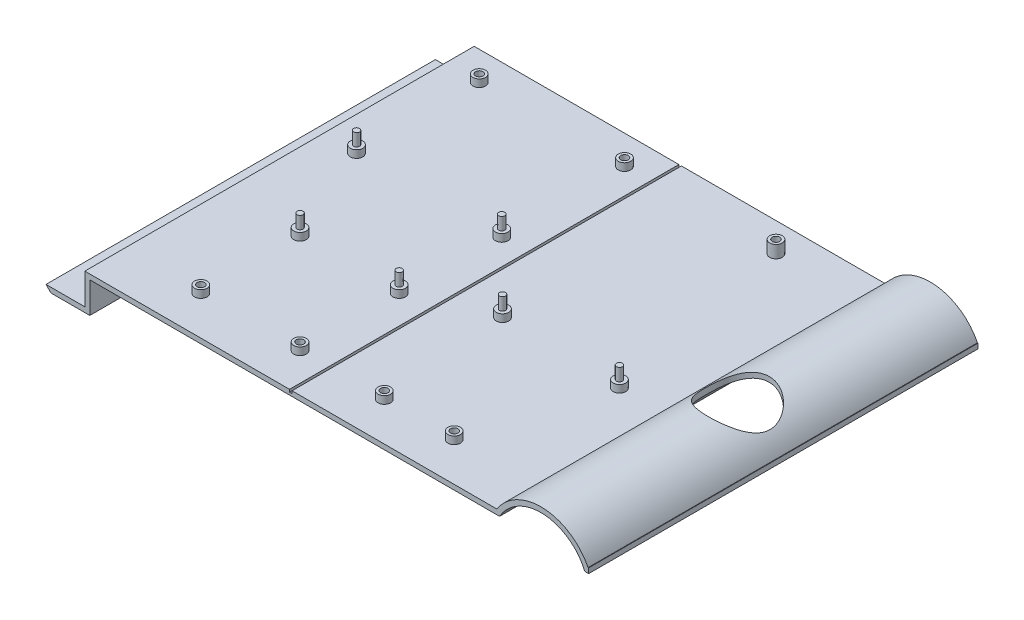
SolidWorks part; units mm, degrees
ref_plane "Ebene vorne" through (0, 0, 0) normal (0, 0, 1) x (1, 0, 0)
ref_plane "Ebene oben" through (0, 0, 0) normal (0, 1, 0) x (1, 0, 0)
ref_plane "Ebene rechts" through (0, 0, 0) normal (1, 0, 0) x (0, 0, -1)
sketch "Skizze5" plane through (0, 0, 0) normal (0, 0, 1) x (1, 0, 0)
  line L0 (0, 0) -> (158.2131, 0)
  line L2 (158.2131, 0) -> (163.627, 0)
  line L3 (0, 0) -> (0, -12.3404)
  line L4 (0, -12.3404) -> (-17.5, -12.3404)
  line L5 (197.6943, -2.0448) -> (199.1943, -2.0448)
  arc A5 (197.6943, -2.0448) -> (181.1299, 9.5495) centre (180.1533, -9.4754) ccw
  arc A6 (181.1299, 9.5495) -> (163.627, 0) centre (180.1533, -9.4754) ccw
  dimension "D1" = 1.5
  dimension "D2" = 17.5
extrude "Linear-Austragen-Dünn1" add sketch "Skizze5" along normal blind 155.5 thin contours L4 L3 L0 thin type one direction reverse wall 2
sketch "Skizze7" plane through (0.013, 0, 0) normal (0, 1, 0) x (1, 0, 0)
  circle A0 centre (11.5, -11.5) radius 2.5
  circle A1 centre (69.5, -11.5) radius 2.5
  circle A2 centre (11.5, -60.5) radius 2.5
  circle A3 centre (69.5, -60.5) radius 2.5
extrude "Aufsatz-Linear austragen3" add sketch "Skizze7" along normal blind 5
sketch "Skizze8" plane through (0, 5, 0) normal (0, 1, 0) x (1, 0, 0)
  circle A0 centre (11.513, -11.5) radius 1.5
extrude "Schnitt-Linear austragen1" cut sketch "Skizze8" against normal blind 8
sketch "Skizze10" plane through (0, 5, 0) normal (0, 1, 0) x (1, 0, 0)
  circle A0 centre (11.513, -60.5) radius 1.2
sketch "Skizze11" plane through (0, 5, 0) normal (0, 1, 0) x (1, 0, 0)
  circle A0 centre (69.513, -60.5) radius 1.2
sketch "Skizze12" plane through (0, 5, 0) normal (0, 1, 0) x (1, 0, 0)
  circle A0 centre (69.513, -11.5) radius 1.5
extrude "Schnitt-Linear austragen4" cut sketch "Skizze12" against normal blind 8
sketch "Skizze13" plane through (0.013, 0, 0) normal (0, 1, 0) x (1, 0, 0)
  line L0 (97.4, -88.1) -> (97.4, -87.1) construction
  line L1 (145.2, -89.2) -> (145.2, -88.2) construction
  line L2 (102.1, -140) -> (102.1, -139) construction
  line L3 (130, -140) -> (130, -139) construction
  circle A0 centre (130, -140) radius 2.5
  circle A1 centre (102.1, -140) radius 2.5
  circle A2 centre (145.2, -89.2) radius 2.5
  circle A3 centre (97.4, -88.1) radius 2.5
  dimension "D1" = 1
  dimension "D2" = 1
  dimension "D3" = 1
  dimension "D4" = 1
extrude "Aufsatz-Linear austragen5" add sketch "Skizze13" along normal blind 5
sketch "Skizze14" plane through (0, 5, 0) normal (0, 1, 0) x (1, 0, 0)
  circle A1 centre (145.213, -89.2) radius 1.2
sketch "Skizze15" plane through (0, 5, 0) normal (0, 1, 0) x (1, 0, 0)
  circle A0 centre (97.413, -88.1) radius 1.2
sketch "Skizze16" plane through (0, 5, 0) normal (0, 1, 0) x (1, 0, 0)
  circle A0 centre (102.113, -140) radius 1.5
extrude "Schnitt-Linear austragen9" cut sketch "Skizze16" against normal blind 8
sketch "Skizze17" plane through (0, 5, 0) normal (0, 1, 0) x (1, 0, 0)
  circle A0 centre (130.013, -140) radius 1.5
extrude "Schnitt-Linear austragen10" cut sketch "Skizze17" against normal blind 8
sketch "Skizze18" plane through (0.013, 0, 0) normal (0, 1, 0) x (1, 0, 0)
  line L0 (28.831, -100.4) -> (28.831, -99.4) construction
  line L1 (68.431, -100.4) -> (68.431, -99.4) construction
  line L2 (28.831, -140) -> (28.831, -139) construction
  line L3 (68.431, -140) -> (68.431, -139) construction
  circle A0 centre (68.431, -140) radius 2.5
  circle A2 centre (28.831, -140) radius 2.5
  circle A3 centre (28.831, -100.4) radius 2.5
  circle A4 centre (68.431, -100.4) radius 2.5
  dimension "D1" = 1
  dimension "D2" = 1
  dimension "D3" = 1
  dimension "D4" = 1
extrude "Aufsatz-Linear austragen6" add sketch "Skizze18" along normal blind 5
sketch "Skizze19" plane through (0, 5, 0) normal (0, 1, 0) x (1, 0, 0)
  circle A0 centre (68.444, -100.4) radius 1.2
sketch "Skizze20" plane through (0, 5, 0) normal (0, 1, 0) x (1, 0, 0)
  circle A0 centre (28.844, -100.4) radius 1.2
sketch "Skizze21" plane through (0, 5, 0) normal (0, 1, 0) x (1, 0, 0)
  circle A0 centre (28.844, -140) radius 1.5
extrude "Schnitt-Linear austragen13" cut sketch "Skizze21" against normal blind 8
sketch "Skizze22" plane through (0, 5, 0) normal (0, 1, 0) x (1, 0, 0)
  circle A0 centre (68.444, -140) radius 1.5
extrude "Schnitt-Linear austragen14" cut sketch "Skizze22" against normal blind 8
extrude "Aufsatz-Linear austragen7" add sketch "Skizze20" along normal blind 5
extrude "Aufsatz-Linear austragen8" add sketch "Skizze19" along normal blind 5
extrude "Aufsatz-Linear austragen9" add sketch "Skizze15" along normal blind 5
extrude "Aufsatz-Linear austragen11" add sketch "Skizze14" along normal blind 5
extrude "Aufsatz-Linear austragen12" add sketch "Skizze10" along normal blind 5
extrude "Aufsatz-Linear austragen13" add sketch "Skizze11" along normal blind 5
sketch "Sketch3" plane through (0, 0, 0) normal (0, 0, -1) x (-1, 0, 0)
  line L0 (17.5, -10.3404) -> (15.5, -12.3404)
  line L1 (17.5, -12.3404) -> (0, -12.3404) construction
  line L2 (15.5, -12.3404) -> (17.5, -12.3404)
  line L3 (17.5, -12.3404) -> (17.5, -10.3404)
extrude "Cut-Extrude2" cut sketch "Sketch3" against normal through all
sketch "Skizze23" plane through (0, 2, 0) normal (0, 1, 0) x (1, 0, 0)
  circle A0 centre (181, -77.85) radius 13
extrude "Schnitt-Linear austragen15" cut sketch "Skizze23" along normal blind 13
sketch "Sketch5" plane through (0, 2, 0) normal (0, 1, 0) x (1, 0, 0)
  line L0 (80.2531, 0) -> (80.2531, -155.5)
  line L1 (-2, 0) -> (162.5063, 0) construction
  line L2 (-2, -155.5) -> (162.5063, -155.5) construction
extrude "Cut-Extrude-Thin1" cut sketch "Sketch5" against normal blind 1 thin thin type mid plane wall 1
sketch "Sketch6" plane through (0, 2, 0) normal (0, 1, 0) x (1, 0, 0)
  line L0 (128.6245, -9.1262) -> (131.4015, -13.8738) construction
  line L6 (132.7719, -13.0721) -> (132.754, -9.8968)
  line L7 (132.754, -9.8968) -> (129.995, -8.3246)
  line L8 (129.995, -8.3246) -> (127.2541, -9.9279)
  line L9 (127.2541, -9.9279) -> (127.272, -13.1032)
  line L10 (127.272, -13.1032) -> (130.031, -14.6754)
  line L11 (130.031, -14.6754) -> (132.7719, -13.0721)
  line L12 (132.7719, -13.0721) -> (132.754, -9.8968) construction
  line L13 (132.754, -9.8968) -> (129.995, -8.3246) construction
  line L14 (129.995, -8.3246) -> (127.2541, -9.9279) construction
  line L15 (127.2541, -9.9279) -> (127.272, -13.1032) construction
  line L16 (127.272, -13.1032) -> (130.031, -14.6754) construction
  line L17 (130.031, -14.6754) -> (132.7719, -13.0721) construction
  circle A0 centre (130.013, -11.5) radius 2.5
  circle A1 centre (130.013, -11.5) radius 1.5
  dimension "D2" = 3
  dimension "D3" = 5
  dimension "D1" = 0
extrude "Boss-Extrude1" add sketch "Sketch6" along normal blind 5
sketch "Sketch7" plane through (0, 2, 0) normal (0, 1, 0) x (1, 0, 0)
  circle A0 centre (130.013, -11.5) radius 1.5
extrude "Cut-Extrude3" cut sketch "Sketch7" against normal up to vertex
